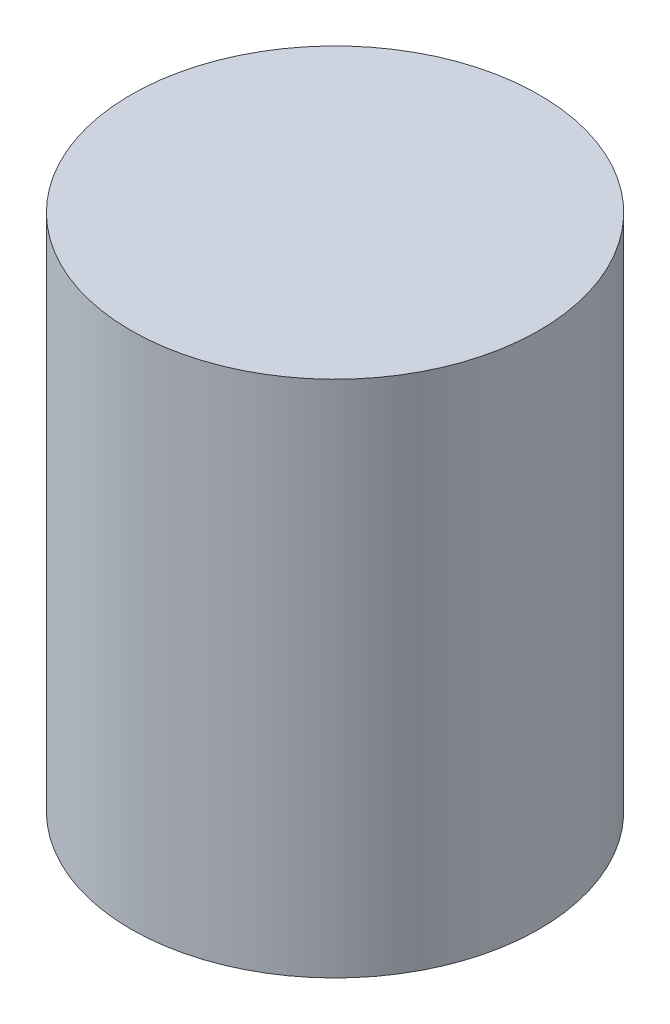
SolidWorks part; units mm, degrees
material "AISI 1020"
ref_plane "Front Plane" through (0, 0, 0) normal (0, 0, 1) x (1, 0, 0)
ref_plane "Top Plane" through (0, 0, 0) normal (0, 1, 0) x (1, 0, 0)
ref_plane "Right Plane" through (0, 0, 0) normal (1, 0, 0) x (0, 0, -1)
sketch "Sketch1" plane through (0, 0, 0) normal (0, 1, 0) x (1, 0, 0)
  circle A0 centre (0, 0) radius 11
extrude "Boss-Extrude1" add sketch "Sketch1" along normal blind 27.94
ref_plane "Plane1" through (0, 12.954, 0) normal (0, 1, 0) x (1, 0, 0)
sketch "Sketch2" plane through (0, 12.954, 0) normal (0, 1, 0) x (1, 0, 0)
  line L0 (-17.2394, 14.5634) -> (-16.2838, -14.8408)
  line L1 (-16.2838, -14.8408) -> (21.4061, -16.2957)
  line L2 (21.4061, -16.2957) -> (22.0943, 14.1973)
  line L3 (22.0943, 14.1973) -> (19.8877, 14.5634)
  circle A0 centre (0, 0) radius 10.4267
  arc A1 (-17.2394, 14.5634) -> (19.8877, 14.5634) centre (1.3242, -556.5965) cw
  dimension "D1" = 20.8534
extrude "Cut-Extrude1" cut sketch "Sketch2" against normal blind 1.1684
sketch "Sketch3" plane through (0, 0, 0) normal (0, -1, 0) x (1, 0, 0)
  circle A0 centre (0, 0) radius 11
extrude "Boss-Extrude2" add sketch "Sketch3" against normal blind 20.32
